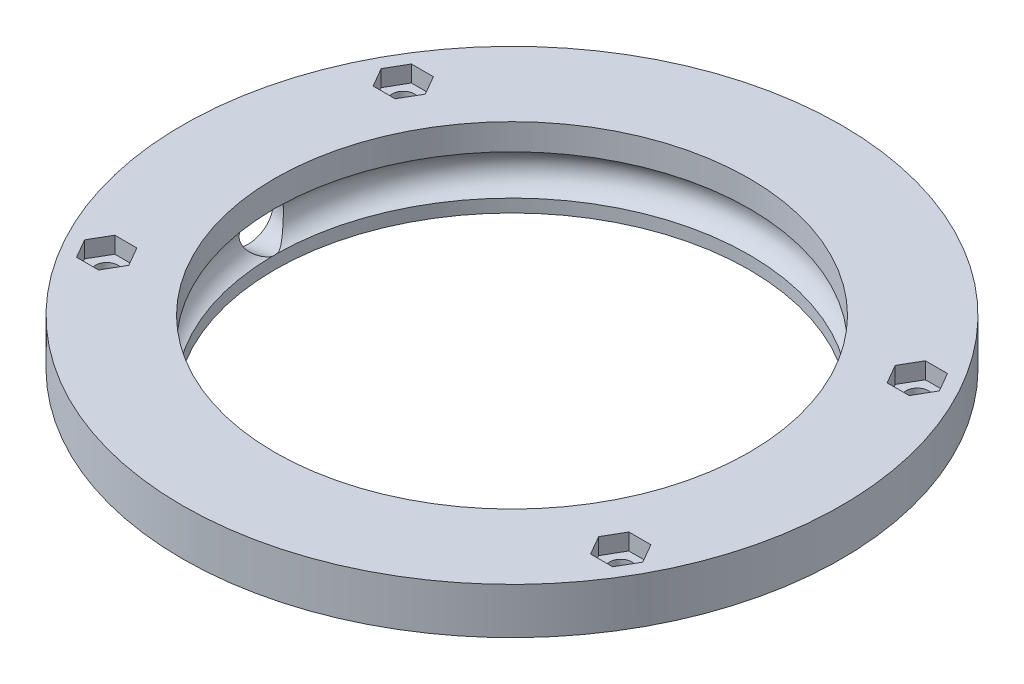
SolidWorks part; units mm, degrees
material "PLA"
ref_plane "Alzado" through (0, 0, 0) normal (0, 0, 1) x (1, 0, 0)
ref_plane "Planta" through (0, 0, 0) normal (0, 1, 0) x (1, 0, 0)
ref_plane "Vista lateral" through (0, 0, 0) normal (1, 0, 0) x (0, 0, -1)
sketch "Croquis1" plane through (0, 0, 0) normal (0, 0, 1) x (1, 0, 0)
  line L0 (50, 12) -> (36, 12)
  line L1 (36, 12) -> (36, 8.0397)
  line L2 (36, 0) -> (40, 0)
  line L3 (40, 0) -> (40, 5)
  line L4 (40, 5) -> (50, 5)
  line L5 (50, 5) -> (50, 12)
  line L6 (36, 1.9603) -> (36, 0)
  line L7 (0, 9.6717) -> (0, -16.2807) construction
  arc A0 (36, 1.9603) -> (36, 8.0397) centre (35, 5) ccw
  dimension "D5" = 3.2
  dimension "D1" = 1
  dimension "D2" = 7
  dimension "D3" = 7
  dimension "D4" = 5
  dimension "D6" = 36
  dimension "D7" = 40
  dimension "D8" = 50
revolve "Revolución1" add sketch "Croquis1" angle 360 about L7
ref_plane "Plano1" through (0, 5, 0) normal (0, 1, 0) x (1, 0, 0)
sketch "Croquis2" plane through (0, 5, 0) normal (0, 1, 0) x (1, 0, 0)
  line L0 (-35.5, 0) -> (-51.5, 0)
  line L1 (-51.5, 0) -> (-51.5, 3.7)
  line L2 (-51.5, 3.7) -> (-40.5, 3.7)
  line L3 (-40.5, 3.7) -> (-35.5, 3)
  line L4 (-35.5, 3) -> (-35.5, 0)
  line L5 (-54.9554, 0) -> (0, 0) construction
  dimension "D1" = 35.5
  dimension "D2" = 3
  dimension "D3" = 3.7
  dimension "D4" = 11
  dimension "D5" = 5
revolve "Cortar-Revolución1" cut sketch "Croquis2" angle 360 about L5
sketch "Croquis4" plane through (0, 12, 0) normal (0, 1, 0) x (1, 0, 0)
  line L1 (39, -22.5) -> (-39, -22.5) construction
  line L2 (39, -22.5) -> (39, 22.5) construction
  line L3 (39, 22.5) -> (-39, 22.5) construction
  line L4 (-39, -22.5) -> (-39, 22.5) construction
  line L5 (39, -22.5) -> (-39, 22.5) construction
  line L6 (39, 22.5) -> (-39, -22.5) construction
  circle A0 centre (-39, 22.5) radius 1.7
  circle A1 centre (39, 22.5) radius 1.7
  circle A2 centre (39, -22.5) radius 1.7
  circle A3 centre (-39, -22.5) radius 1.7
  point P0 (0, 0)
  dimension "D1" = 3.4
  dimension "D2" = 78
  dimension "D3" = 45
extrude "Cortar-Extruir1" cut sketch "Croquis4" against normal blind 10
sketch "Croquis5" plane through (0, 12, 0) normal (0, 1, 0) x (1, 0, 0)
  line L0 (-35.9975, 0) -> (36, 0) construction
  line L1 (-42.35, 22.5) -> (-40.675, 19.5988)
  line L2 (-40.675, 19.5988) -> (-37.325, 19.5988)
  line L3 (-37.325, 19.5988) -> (-35.65, 22.5)
  line L4 (-35.65, 22.5) -> (-37.325, 25.4012)
  line L5 (-37.325, 25.4012) -> (-40.675, 25.4012)
  line L6 (-40.675, 25.4012) -> (-42.35, 22.5)
  line L7 (-42.35, -22.5) -> (-40.675, -25.4012)
  line L8 (-40.675, -25.4012) -> (-37.325, -25.4012)
  line L9 (-37.325, -25.4012) -> (-35.65, -22.5)
  line L10 (-35.65, -22.5) -> (-37.325, -19.5988)
  line L11 (-37.325, -19.5988) -> (-40.675, -19.5988)
  line L12 (-40.675, -19.5988) -> (-42.35, -22.5)
  line L13 (35.65, 22.5) -> (37.325, 19.5988)
  line L14 (37.325, 19.5988) -> (40.675, 19.5988)
  line L15 (40.675, 19.5988) -> (42.35, 22.5)
  line L16 (42.35, 22.5) -> (40.675, 25.4012)
  line L17 (40.675, 25.4012) -> (37.325, 25.4012)
  line L18 (37.325, 25.4012) -> (35.65, 22.5)
  line L19 (35.65, -22.5) -> (37.325, -25.4012)
  line L20 (37.325, -25.4012) -> (40.675, -25.4012)
  line L21 (40.675, -25.4012) -> (42.35, -22.5)
  line L22 (42.35, -22.5) -> (40.675, -19.5988)
  line L23 (40.675, -19.5988) -> (37.325, -19.5988)
  line L24 (37.325, -19.5988) -> (35.65, -22.5)
  circle A0 centre (-39, 22.5) radius 3.35 construction
  circle A1 centre (-39, -22.5) radius 3.35 construction
  circle A2 centre (39, 22.5) radius 3.35 construction
  circle A3 centre (39, -22.5) radius 3.35 construction
  circle A4 centre (0, 0) radius 36 construction
  dimension "D1" = 6.7
extrude "Cortar-Extruir2" cut sketch "Croquis5" against normal blind 2.5
